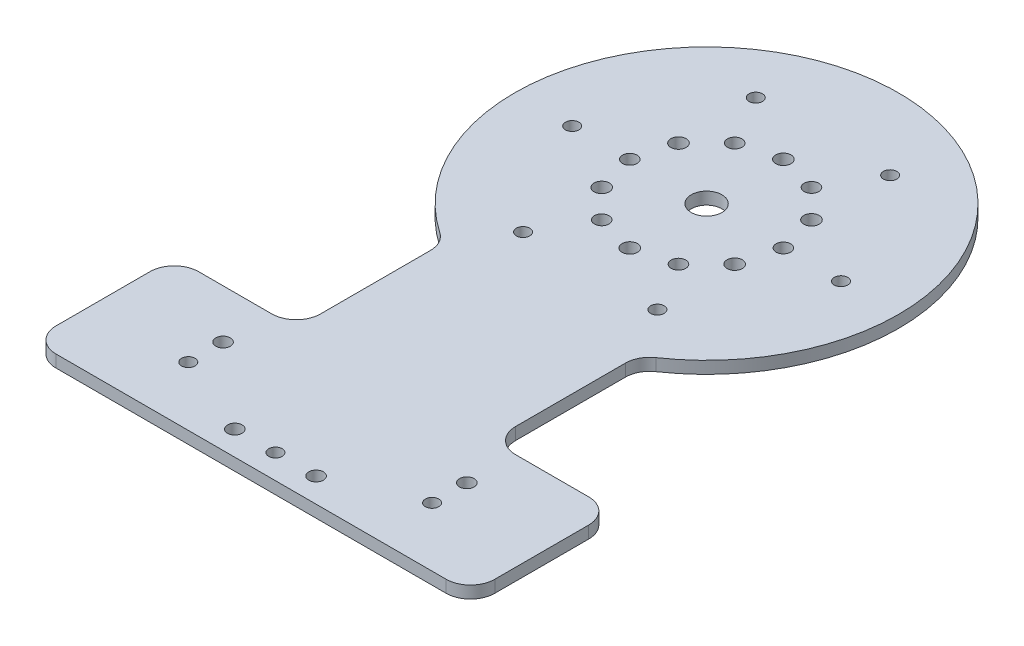
SolidWorks part; units mm, degrees
material "Balsa"
ref_plane "Front" through (0, 0, 0) normal (0, 0, 1) x (1, 0, 0)
ref_plane "Top" through (0, 0, 0) normal (0, 1, 0) x (1, 0, 0)
ref_plane "Right" through (0, 0, 0) normal (1, 0, 0) x (0, 0, -1)
sketch "Sketch1" plane through (0, 0, 0) normal (0, 1, 0) x (1, 0, 0)
  line L0 (150, 0) -> (150, 200) construction
  line L1 (0, 0) -> (300, 0)
  line L2 (0, 0) -> (0, 200)
  line L3 (0, 200) -> (300, 200)
  line L4 (300, 0) -> (300, 200)
  dimension "D2" = 300
  dimension "D6" = 200
extrude "Boss-Extrude1" add sketch "Sketch1" along normal blind 3.175
sketch "Sketch6" plane through (0, 3.175, 0) normal (0, 1, 0) x (1, 0, 0)
  line L0 (150, 118.651) -> (150, 0) construction
  line L1 (0, 0) -> (300, 0) construction
  circle A0 centre (150, 118.651) radius 4
  dimension "D1" = 8
  dimension "D2" = 118.651
extrude "Cut-Extrude2" cut sketch "Sketch6" against normal through all
fillet "Fillet1" radius 6.35 4 edges at (0, 1.5875, 0) (300, 1.5875, 0) (300, 1.5875, -200) (0, 1.5875, -200)
sketch "Sketch2" plane through (0, 3.175, 0) normal (0, 1, 0) x (1, 0, 0)
  line L0 (150, 49.9999) -> (150, 0) construction
  line L1 (6.35, 0) -> (293.65, 0) construction
  line L2 (0, 49.9999) -> (300, 49.9999) construction
  line L3 (0, 193.65) -> (0, 6.35) construction
  line L4 (150, 49.9999) -> (150, 99.9998) construction
  line L5 (50.8, 75.3999) -> (50.8, 49.9999) construction
  line L6 (300, 6.35) -> (300, 193.65) construction
  line L7 (0, 193.65) -> (0, 6.35) construction
  line L8 (293.65, 200) -> (6.35, 200) construction
  line L9 (150, 99.9998) -> (0, 99.9998) construction
  line L10 (0, 193.65) -> (0, 6.35) construction
  circle A0 centre (6.35, 174.6) radius 1.5
  circle A1 centre (6.35, 49.9999) radius 1.5
  circle A2 centre (249.2, 75.3999) radius 1.5
  circle A3 centre (50.8, 75.3999) radius 1.5
  circle A4 centre (293.65, 49.9999) radius 1.5
  circle A5 centre (50.8, 24.5999) radius 1.5
  circle A6 centre (249.2, 24.5999) radius 1.5
  circle A7 centre (25.4, 193.65) radius 1.5
  circle A8 centre (274.6, 193.65) radius 1.5
  circle A9 centre (293.65, 174.6) radius 1.5
  dimension "D1" = 3
  dimension "D8" = 25.4
  dimension "D9" = 25.4
  dimension "D2" = 6.35
  dimension "D3" = 25.4
  dimension "D4" = 50.8
  dimension "D5" = 99.9998
  dimension "D6" = 6.35
  dimension "D7" = 6.35
extrude "Cut-Extrude1" cut sketch "Sketch2" against normal through all
sketch "Sketch16" plane through (0, 3.175, -5.8) normal (0, -1, 0) x (1, 0, 0)
  line L0 (150, -112.851) -> (150, 0) construction
  line L3 (150, -25.001) -> (181.75, -25.001) construction
  line L4 (181.75, -25.001) -> (181.75, -0.551) construction
  line L6 (118.25, -0.551) -> (139.4167, -0.551) construction
  line L7 (139.4167, -0.551) -> (160.5833, -0.551) construction
  line L8 (160.5833, -0.551) -> (181.75, -0.551) construction
  circle A0 centre (150, -112.851) radius 80 construction
  circle A1 centre (150, -112.851) radius 4 construction
  circle A2 centre (150, -25.001) radius 7.85 construction
  circle A3 centre (150, -25.001) radius 6.35 construction
  circle A4 centre (118.25, -18.651) radius 1.8987
  circle A5 centre (118.25, -0.551) radius 1.8987 construction
  circle A6 centre (139.4167, -0.551) radius 1.8987
  circle A7 centre (160.5833, -0.551) radius 1.8987
  circle A8 centre (181.75, -0.551) radius 1.8987 construction
  circle A9 centre (181.75, -18.651) radius 1.8987
  point P0 (181.75, -0.551)
  point P28 (181.75, -18.651)
  point P32 (118.25, -18.651)
  point P33 (118.25, -0.551)
  point P34 (139.4167, -0.551)
  point P36 (160.5833, -0.551)
  dimension "D1" = 160
  dimension "D2" = 1.5
  dimension "D3" = 12.7
  dimension "D7" = 3.7973
  dimension "D4" = 31.75
  dimension "D5" = 24.45
  dimension "D6" = 18.1
extrude "M5_through" cut sketch "Sketch16" along normal through all
sketch "Sketch9" plane through (0, 3.175, 0) normal (0, 1, 0) x (-1, 0, 0)
  line L0 (-118.25, -24.451) -> (-118.25, -6.351) construction
  line L1 (-118.25, -6.351) -> (-181.75, -6.351) construction
  line L2 (-181.75, -6.351) -> (-181.75, -24.451) construction
  circle A0 centre (-118.25, -15.401) radius 1.75
  circle A1 centre (-150, -6.351) radius 1.75
  circle A2 centre (-181.75, -15.401) radius 1.75
  circle A3 centre (-160.5833, -6.351) radius 1.8987 construction
  circle A5 centre (-160.5833, -6.351) radius 1.8987
  point P2 (-150, -6.351)
  dimension "D1" = 3.5
extrude "Cut-Extrude3" cut sketch "Sketch9" against normal through all
sketch "Sketch10" plane through (0, 3.175, 0) normal (0, 1, 0) x (1, 0, 0)
  line L0 (124.6, 75.5831) -> (124.6, 37.151)
  line L1 (124.6, 37.151) -> (92.85, 37.151)
  line L2 (92.85, 37.151) -> (92.85, 0)
  line L3 (6.35, 0) -> (293.65, 0) construction
  line L4 (92.85, 0) -> (207.15, 0) construction
  line L5 (207.15, 0) -> (207.15, 37.151)
  line L6 (207.15, 37.151) -> (175.4, 37.151)
  line L7 (175.4, 37.151) -> (175.4, 75.5831)
  line L8 (150, 118.651) -> (150, 138.651) construction
  line L9 (150, 118.651) -> (167.3205, 128.651) construction
  line L10 (150, 118.651) -> (167.3205, 108.651) construction
  line L11 (92.85, 30.801) -> (207.15, 30.801) construction
  line L12 (105.55, 30.801) -> (105.55, 6.35) construction
  line L13 (150, 0) -> (150, 30.801) construction
  line L14 (92.85, 0) -> (0, 0)
  line L15 (0, 0) -> (0, 200)
  line L16 (0, 200) -> (300, 200)
  line L17 (300, 200) -> (300, 0)
  line L18 (300, 0) -> (207.15, 0)
  line L19 (300, 6.35) -> (300, 193.65) construction
  line L20 (293.65, 200) -> (6.35, 200) construction
  line L21 (150, 118.651) -> (160, 135.9715) construction
  circle A0 centre (150, 118.651) radius 80 construction
  arc A1 (175.4, 75.5831) -> (124.6, 75.5831) centre (150, 118.651) ccw
  circle A2 centre (118.25, 24.451) radius 1.8987 construction
  circle A3 centre (160, 135.9715) radius 1.8987
  circle A4 centre (150, 138.651) radius 1.9939
  circle A5 centre (167.3205, 128.651) radius 1.9939
  circle A6 centre (167.3205, 108.651) radius 1.9939
  circle A7 centre (150, 98.651) radius 1.9939
  circle A8 centre (132.6795, 108.651) radius 1.9939
  circle A9 centre (132.6795, 128.651) radius 1.9939
  circle A10 centre (105.55, 30.801) radius 1.9939 construction
  circle A11 centre (105.55, 6.35) radius 1.9939 construction
  circle A12 centre (194.45, 6.35) radius 1.9939 construction
  circle A13 centre (194.45, 30.801) radius 1.9939 construction
  circle A14 centre (181.75, 24.451) radius 1.8987 construction
  circle A15 centre (170, 118.651) radius 1.8987
  circle A16 centre (160, 101.3305) radius 1.8987
  circle A17 centre (140, 101.3305) radius 1.8987
  circle A18 centre (130, 118.651) radius 1.8987
  circle A19 centre (140, 135.9715) radius 1.8986
  point P64 (150, 118.651)
  dimension "D1" = 160
  dimension "D2" = 50
  dimension "D8" = 3.9878
  dimension "D9" = 6.35
  dimension "D12" = 3.7973
  dimension "D3" = 25.4
  dimension "D4" = 12.7
  dimension "D5" = 50.8
  dimension "D7" = 20
  dimension "D10" = 6.35
  dimension "D11" = 12.7
  dimension "D13" = 20
  dimension "D14" = 30
  dimension "D6" = 6
  dimension "D15" = 6
extrude "Cut-Extrude5" cut sketch "Sketch10" against normal through all
sketch "Sketch17" plane through (0, 3.175, 0) normal (0, 1, 0) x (1, 0, 0)
  line L0 (150, 118.651) -> (185, 118.651) construction
  line L1 (132.5, 148.9619) -> (150, 118.651) construction
  line L2 (150, 118.651) -> (167.5, 148.9619) construction
  circle A0 centre (185, 118.651) radius 1.75
  circle A1 centre (167.5, 88.3401) radius 1.75
  circle A2 centre (132.5, 88.3401) radius 1.75
  circle A3 centre (115, 118.651) radius 1.75
  circle A4 centre (132.5, 148.9619) radius 1.75
  circle A5 centre (167.5, 148.9619) radius 1.75
  dimension "D1" = 3.5
  dimension "D2" = 35
extrude "M3-through" cut sketch "Sketch17" against normal through all
fillet "Fillet2" radius 6.35 8 edges at (92.85, 1.5875, 0) (207.15, 1.5875, 0) (207.15, 1.5875, -37.151) (175.4, 1.5875, -37.151) (175.4, 1.5875, -75.5831) (124.6, 1.5875, -75.5831) (92.85, 1.5875, -37.151) (124.6, 1.5875, -37.151)
other "Move Face1" [suppressed] parameters "D1"=0.08
